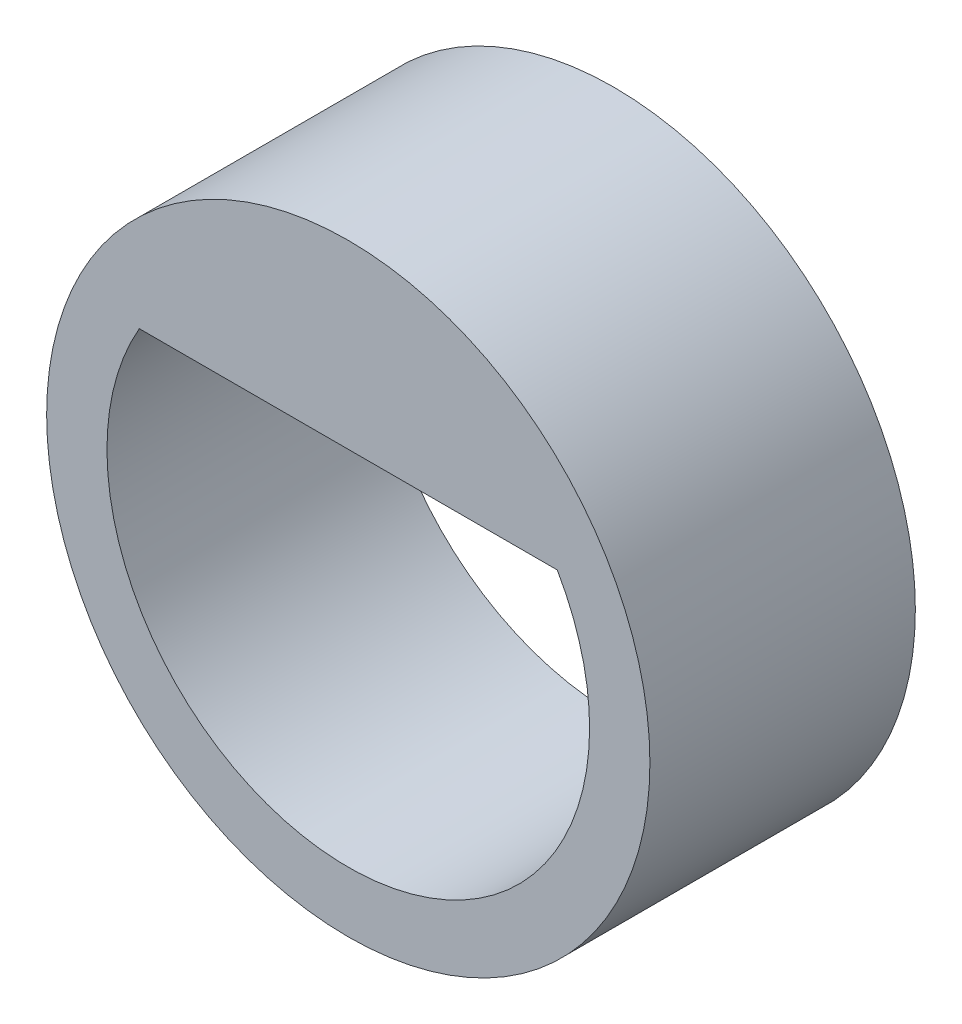
SolidWorks part; units mm, degrees
ref_plane "Front Plane" through (0, 0, 0) normal (0, 0, 1) x (1, 0, 0)
ref_plane "Top Plane" through (0, 0, 0) normal (0, 1, 0) x (1, 0, 0)
ref_plane "Right Plane" through (0, 0, 0) normal (1, 0, 0) x (0, 0, -1)
sketch "Sketch1" plane through (0, 0, 0) normal (0, 0, 1) x (1, 0, 0)
  line L0 (-1.7321, 1) -> (1.7321, 1)
  circle A0 centre (0, 0) radius 2.5
  arc A1 (-1.7321, 1) -> (1.7321, 1) centre (0, 0) ccw
  point P3 (0, -2)
  dimension "D1" = 5
  dimension "D2" = 0.5
  dimension "D3" = 3
extrude "Boss-Extrude1" add sketch "Sketch1" along normal blind 2.2
